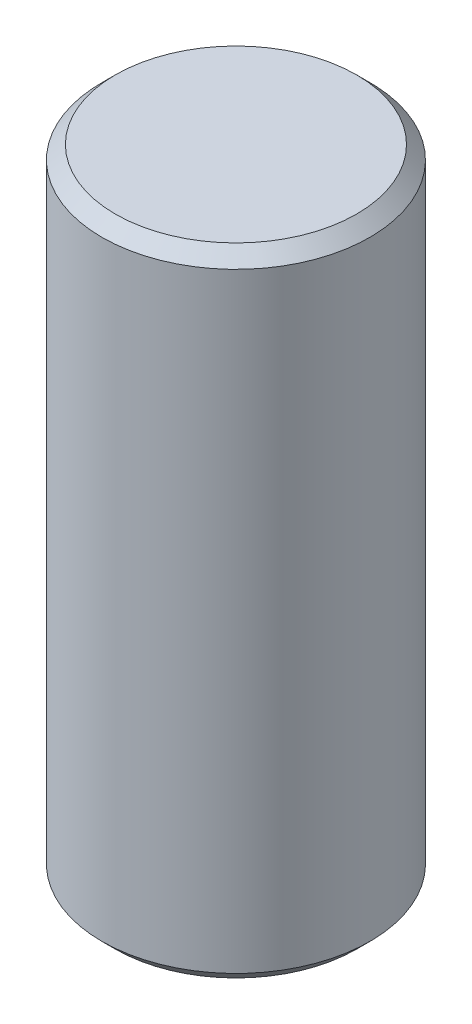
SolidWorks part; units mm, degrees
ref_plane "Front Plane" through (0, 0, 0) normal (0, 0, 1) x (1, 0, 0)
ref_plane "Top Plane" through (0, 0, 0) normal (0, 1, 0) x (1, 0, 0)
ref_plane "Right Plane" through (0, 0, 0) normal (1, 0, 0) x (0, 0, -1)
sketch "Sketch1" plane through (0, 0, 0) normal (0, 1, 0) x (1, 0, 0)
  circle A0 centre (0, 0) radius 0.5
  dimension "D1" = 1
extrude "Boss-Extrude1" add sketch "Sketch1" along normal mid plane 2.375
chamfer "Chamfer1" distance 0.05 angle 45 2 edges at (0, -1.1875, 0.5) (0, 1.1875, 0.5)
